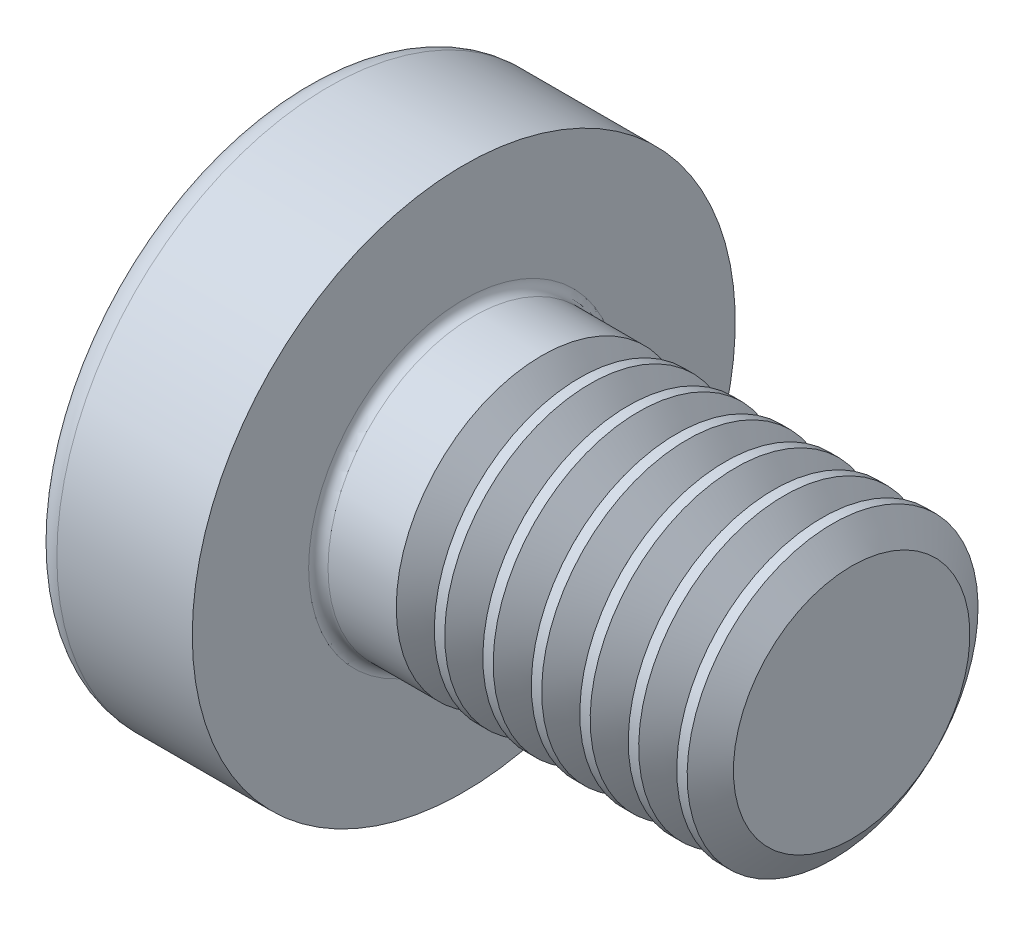
SolidWorks part; units mm, degrees
ref_plane "Plane1" through (0, 0, 0) normal (0, 0, 1) x (1, 0, 0)
ref_plane "Plane2" through (0, 0, 0) normal (0, 1, 0) x (1, 0, 0)
ref_plane "Plane3" through (0, 0, 0) normal (1, 0, 0) x (0, 0, -1)
sketch "BodySke" plane through (0, 0, 0) normal (0, 0, 1) x (1, 0, 0)
  line L0 (2.4, 1.5) -> (2.4, 2.8)
  line L1 (2.65, 6.35) -> (2.65, -3.175) construction
  line L2 (-25.4, 0) -> (127, 0) construction
  line L3 (6.4, 0) -> (0, 0)
  line L4 (2.4, 1.5) -> (6.4, 1.5)
  line L5 (6.4, 1.5) -> (6.4, 0)
  line L6 (1.0035, 2.8) -> (2.4, 2.8)
  line L8 (2.4, 6.35) -> (2.4, -3.175) construction
  arc A0 (0.7754, 2.6744) -> (0, 0) centre (5, 0) ccw
  arc A2 (0.7754, 2.6744) -> (1.0035, 2.8) centre (1.0035, 2.53) cw
  dimension "Head_crown_rad" = 5
  dimension "Head_fillet_rad" = 0.27
  dimension "Length" = 4
  dimension "Head_ht" = 2.4
  dimension "Head_dia" = 5.6
  dimension "Advance" = 0.5
  dimension "Thread_nom" = 4
  dimension "Diameter" = 3
revolve "Base-Revolve" add sketch "BodySke"
cosmetic thread "ThreadCosmetic" [suppressed]
fillet "Fillet1" radius 0.1 1 edges at (2.4, 0, 1.5)
sketch "Sketch3" plane through (0, 0, 0) normal (1, 0, 0) x (0, 0, -1)
  line L0 (0.37, -1.4) -> (-0.37, -1.4)
  line L1 (0.37, -1.4) -> (0.37, 1.4)
  line L2 (-0.37, 1.4) -> (0.37, 1.4)
  line L3 (-0.37, 1.4) -> (-0.37, -1.4)
  dimension "Cross_dia" = 2.8
  dimension "D1" = 1.4
  dimension "Cross_width" = 0.74
  dimension "D2" = 0.37
ref_plane "Plane4" through (1.75, 0, 0) normal (1, 0, 0) x (0, 0, -1)
sketch "Sketch4" plane through (1.75, 0, 0) normal (1, 0, 0) x (0, 0, -1)
  line L0 (0.37, -0.5275) -> (-0.37, -0.5275)
  line L1 (0.37, -0.5275) -> (0.37, 0.5275)
  line L2 (-0.37, 0.5275) -> (0.37, 0.5275)
  line L3 (-0.37, 0.5275) -> (-0.37, -0.5275)
  dimension "D1" = 0.74
  dimension "D2" = 1.055
  dimension "D3" = 0.37
  dimension "D4" = 0.5275
loft "Recess" cut profiles "Sketch3", "Sketch4"
pattern_circular "RecPat" count 2 every 90 about axis through (0, 0, 0) along (1, 0, 0) of "Recess"
sketch "RecCorSke" plane through (0, 0, 0) normal (0, 0, 1) x (1, 0, 0)
  line L0 (-3.175, 0) -> (15.875, 0) construction
  line L1 (-25.4, 0) -> (127, 0) construction
  line L2 (0, 0) -> (0, 0.6784)
  line L3 (0, 0.6784) -> (1.75, 0.556)
  line L4 (1.75, 0.556) -> (1.9307, 0)
  line L5 (1.9307, 0) -> (0, 0)
  dimension "Diameter" = 1.112
  dimension "Depth" = 1.75
  dimension "Draft_angle" = 4
  dimension "Bottom_angle" = 18
revolve "RecessCore" cut sketch "RecCorSke" angle 360 about L0
sketch "ThdSchSke" plane through (0, 0, 0) normal (0, 0, 1) x (1, 0, 0)
  line L0 (3.4, -1.2195) -> (3.2036, -1.5)
  line L1 (3.4, -1.2195) -> (3.5964, -1.5)
  line L2 (3.5964, -1.5) -> (3.5964, -1.875)
  line L3 (-3.175, 0) -> (5.1513, 0) construction
  line L5 (3.5964, -1.875) -> (3.2036, -1.875)
  line L6 (3.2036, -1.875) -> (3.2036, -1.5)
  dimension "Diameter" = 3
  dimension "SideAngle" = 55
  dimension "VeeAngle" = 70
  dimension "Thread_minor" = 2.439
  dimension "Overcut" = 3.75
  dimension "Start" = 3.4
revolve "ThreadSchematic" cut sketch "ThdSchSke" angle 360 about L3
pattern_linear "ThdSchPat" count 7 spacing 0.5 along (1, 0, 0) of "ThreadSchematic"
equation "\"D1@Sketch3\" = \"Cross_dia@Sketch3\" / 2"
equation "\"D2@Sketch3\" = \"Cross_width@Sketch3\" / 2"
equation "\"Depth@RecCorSke\" = \"Cross_depth@Plane4\""
equation "\"D1@Sketch4\" = \"Cross_width@Sketch3\""
equation "\"D2@Sketch4\" = \"Cross_dia@Sketch3\" - 2.0 * \"Cross_depth@Plane4\" * tan(26.5  * 0.017453292)"
equation "\"D3@Sketch4\" = \"D1@Sketch4\" / 2"
equation "\"D4@Sketch4\" = \"D2@Sketch4\" / 2"
equation "\"Thread_length@ThreadCosmetic\" = ((sgn( (\"Length@BodySke\" - \"Advance@BodySke\" * 2.0 ) - \"Thread_nom@BodySke\" )-1)*( (\"Length@BodySke\" - \"Advance@BodySke\" * 2.0 ) - \"Thread_nom@BodySke\" ))/-2+ \"Thread_nom@BodySke\""
equation "\"Thread_minor@ThdSchSke\" = \"Thread_minor@ThreadCosmetic\""
equation "\"Diameter@ThdSchSke\" = \"Diameter@BodySke\""
equation "\"Overcut@ThdSchSke\" = \"Diameter@BodySke\" * 1.25"
equation "\"Start@ThdSchSke\" = \"Head_ht@BodySke\" + \"Length@BodySke\" - \"Thread_length@ThreadCosmetic\"  '---Non-countersunk---"
equation "\"Num_threads@ThdSchPat\" = int( \"Thread_length@ThreadCosmetic\" / \"Advance@BodySke\" + 0.999 )  + 1"
equation "\"Advance@ThdSchPat\" = \"Thread_length@ThreadCosmetic\" /  (\"Num_threads@ThdSchPat\" - 1) 'relax it"
